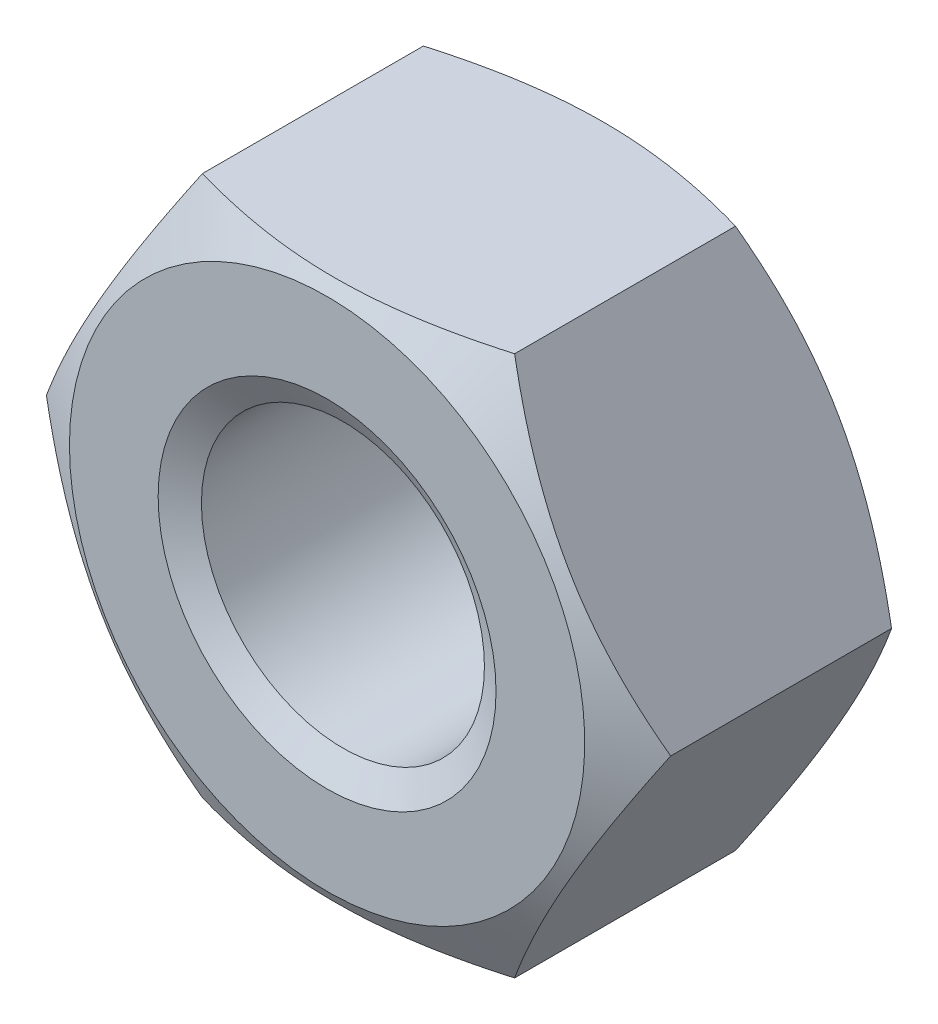
SolidWorks part; units mm, degrees
ref_plane "Front" through (0, 0, 0) normal (0, 0, 1) x (1, 0, 0)
ref_plane "Top" through (0, 0, 0) normal (0, 1, 0) x (1, 0, 0)
ref_plane "Right" through (0, 0, 0) normal (1, 0, 0) x (0, 0, -1)
sketch "Sketch1" plane through (0, 0, 0) normal (0, 0, 1) x (1, 0, 0)
  line L1 (9.2376, 0) -> (4.6188, 8)
  line L2 (4.6188, 8) -> (-4.6188, 8)
  line L3 (-4.6188, 8) -> (-9.2376, 0)
  line L4 (-9.2376, 0) -> (-4.6188, -8)
  line L5 (-4.6188, -8) -> (4.6188, -8)
  line L6 (4.6188, -8) -> (9.2376, 0)
  circle A0 centre (0, 0) radius 8 construction
  circle A1 centre (0, 0) radius 4.188
  dimension "D" = 8.376
  dimension "s" = 16
extrude "BaseNut" add sketch "Sketch1" against normal blind 8.4
cosmetic thread "ThreadCosmetic1" parameters "D"=10
sketch "Sketch2" plane through (0, 0, 0) normal (0, 1, 0) x (1, 0, 0)
  line L0 (-9.2376, 8.4) -> (-7.625, 8.4)
  line L2 (-7.625, 8.4) -> (-9.2376, 7.469)
  line L3 (-9.2376, 7.469) -> (-9.2376, 8.4)
  line L4 (0, 3.3759) -> (0, -9.8171) construction
  line L6 (-9.7712, 4.2) -> (9.8853, 4.2) construction
  line L7 (-9.2376, 0.931) -> (-9.2376, 0)
  line L8 (-7.625, 0) -> (-9.2376, 0.931)
  line L9 (-9.2376, 0) -> (-7.625, 0)
  dimension "dw" = 15.25
  dimension "D1" = 30
  dimension "D2" = 4.2
revolve "Double-Chamfer" cut sketch "Sketch2" angle 360 about L4
chamfer "EndChamfer" distance 0.812 angle 30 2 edges at (4.188, 0, -8.4) (4.188, 0, 0)
sketch "Sketch3" plane through (0, 0, 0) normal (0, 1, 0) x (1, 0, 0)
  line L0 (-4.8912, 7.588) -> (-4.188, 7.182)
  line L1 (-4.188, 7.182) -> (-3.376, 7.182)
  line L2 (-3.376, 7.182) -> (-3.376, 7.994)
  line L3 (-3.376, 7.994) -> (-4.188, 7.994)
  line L4 (-4.188, 7.994) -> (-4.8912, 7.588)
  line L5 (0, 7.4383) -> (0, 16.8806) construction
  dimension "D1" = 0.812
  dimension "D2" = 8.376
revolve "Cut-Revolve10" [suppressed] cut sketch "Sketch3" angle 360 about L5
pattern_linear "LPattern10" [suppressed] count 9 spacing 0.9744 along (0, 0, -1)
equation "\"dw@Sketch2\" = \"s@Sketch1\"-0.75"
equation "\"D2@Sketch2\" = \"m@BaseNut\" / 2"
equation "\"D2@Sketch3\" = \"D@Sketch1\""
equation "\"D1@Sketch3\" =  (\"D@ThreadCosmetic1\"   - \"D@Sketch1\")  / 2"
equation "\"D3@LPattern10\" = \"D1@Sketch3\" * 1.2"
equation "\"D1@LPattern10\" = \"m@BaseNut\"/\"D3@LPattern10\""
